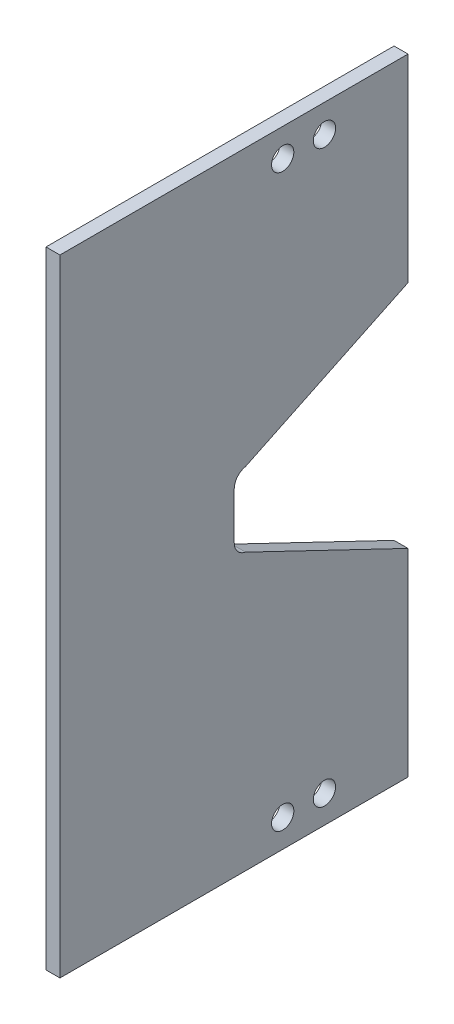
SolidWorks part; units mm, degrees
material "ABS"
ref_plane "前视基准面" through (0, 0, 0) normal (0, 0, 1) x (1, 0, 0)
ref_plane "上视基准面" through (0, 0, 0) normal (0, 1, 0) x (1, 0, 0)
ref_plane "右视基准面" through (0, 0, 0) normal (1, 0, 0) x (0, 0, -1)
ref_plane "基准面4" through (-0.7938, 0, 0) normal (-1, 0, 0) x (0, -1, 0)
sketch "草图1" plane through (-0.7938, 0, 0) normal (-1, 0, 0) x (0, -1, 0)
  line L1 (38.795, 5) -> (12.795, 5)
  line L2 (10.795, 3) -> (10.795, -13)
  line L5 (10.795, 3) -> (55.77, 3) construction
  line L6 (55.77, 3) -> (55.77, -5.0783) construction
  line L7 (55.77, 3) -> (55.77, 5) construction
  line L13 (38.795, 5) -> (72.745, 5)
  line L15 (100.745, 3) -> (100.745, -13)
  line L18 (72.745, 5) -> (98.745, 5)
  line L19 (55.77, 5) -> (55.77, -5.0783) construction
  line L20 (55.77, -5.0783) -> (55.77, -0.0391) construction
  line L21 (55.77, -0.0391) -> (65.77, -0.0391) construction
  line L22 (72.112, -14.1547) -> (62.1308, -0.0391) construction
  line L31 (13.295, -15) -> (13.295, -10) construction
  line L32 (13.295, 0) -> (13.295, -15) construction
  line L33 (18.295, 0) -> (18.295, -15) construction
  line L34 (18.295, -15) -> (18.295, -10) construction
  line L35 (93.245, 0) -> (93.245, -15) construction
  line L36 (93.245, -15) -> (93.245, -10) construction
  line L37 (93.245, -10) -> (98.245, -10) construction
  line L38 (55.77, -0.0391) -> (50.77, -0.0391)
  line L39 (55.77, -0.0391) -> (60.77, -0.0391)
  line L40 (12.795, -15) -> (47.795, -15)
  line L41 (98.745, -15) -> (63.745, -15)
  line L42 (50.77, -0.0391) -> (47.795, -15)
  line L43 (60.77, -0.0391) -> (63.745, -15)
  arc A2 (12.795, 5) -> (10.795, 3) centre (12.795, 3) ccw
  arc A3 (10.795, -13) -> (12.795, -15) centre (12.795, -13) ccw
  arc A12 (98.745, 5) -> (100.745, 3) centre (98.745, 3) cw
  arc A13 (100.745, -13) -> (98.745, -15) centre (98.745, -13) cw
extrude "凸台-拉伸1" add sketch "草图1" against normal blind 2
fillet "圆角1" radius 2 1 edges at (0.2063, -47.795, -15)
fillet "圆角2" radius 2 1 edges at (0.2062, -50.77, -0.0391)
fillet "圆角3" radius 2 1 edges at (0.2062, -60.77, -0.0391)
fillet "圆角4" radius 2 1 edges at (0.2063, -63.745, -15)
sketch "草图2" plane through (1.2062, 0, 0) normal (1, 0, 0) x (0, 0, -1)
  line L0 (-5, -55.77) -> (-15, -55.77) construction
  line L2 (-5, -98.745) -> (-5, -12.795) construction
  line L3 (-15, -55.77) -> (-15, -100.745) construction
  line L4 (-15, -100.745) -> (-3, -100.745) construction
  line L5 (-3, -100.745) -> (-3, -10.795) construction
  line L6 (-3, -10.795) -> (-15, -10.795) construction
  line L7 (-15, -10.795) -> (-15, -55.77) construction
  line L8 (-15, -10.795) -> (-3, -10.795)
  line L9 (-3, -10.795) -> (-3, -100.745)
  line L10 (-3, -100.745) -> (-15, -100.745)
  line L11 (-15, -100.745) -> (-15, -10.795)
  line L12 (15, -29.4743) -> (25, -29.4743) construction
  line L13 (15, -12.795) -> (15, -46.1535) construction
  line L14 (25, -29.4743) -> (25, -82.0657) construction
  line L15 (25, -82.0657) -> (15, -82.0657) construction
  line L16 (15, -65.3865) -> (15, -98.745) construction
  line L17 (15, -82.0657) -> (15, -100.745) construction
  line L18 (25, -82.0657) -> (25, -100.745) construction
  line L19 (25, -100.745) -> (13, -100.745) construction
  line L20 (13, -100.745) -> (-3, -100.745) construction
  line L21 (13, -100.745) -> (13, -10.795) construction
  line L22 (13, -10.795) -> (25, -10.795) construction
  line L23 (25, -10.795) -> (25, -29.4743) construction
  line L24 (1.6491, -50.4499) -> (13.3901, -48.1151) construction
  line L25 (13.3901, -48.1151) -> (25, -45.8065) construction
  line L26 (1.6491, -61.0901) -> (13.3901, -63.4249) construction
  line L27 (13.3901, -63.4249) -> (25, -65.7335) construction
  line L28 (13.3901, -48.1151) -> (25, -45.8065)
  line L29 (25, -45.8065) -> (25, -10.795)
  line L30 (25, -10.795) -> (13, -10.795)
  line L31 (13, -10.795) -> (13.3901, -48.1151)
  line L32 (13.3901, -63.4249) -> (25, -65.7335)
  line L33 (25, -65.7335) -> (25, -100.745)
  line L34 (25, -100.745) -> (13, -100.745)
  line L35 (13, -100.745) -> (13.3901, -63.4249)
  arc A0 (13, -100.745) -> (15, -98.745) centre (13, -98.745) ccw construction
extrude "凸台-拉伸2" add sketch "草图2" against normal blind 2
sketch "草图5" plane through (1.2062, 0, 0) normal (1, 0, 0) x (0, 0, -1)
  line L0 (25, -45.8065) -> (25, -10.795) construction
  line L1 (25, -10.795) -> (25, -28.3007) construction
  line L2 (25, -28.3007) -> (25, -45.8065) construction
  line L3 (25, -45.8065) -> (25, -37.0536) construction
  line L4 (25, -37.0536) -> (25, -41.43) construction
  line L5 (25, -41.43) -> (1.6491, -50.4499) construction
  line L7 (1.6491, -50.4499) -> (25, -45.8065)
  line L9 (0.0391, -55.77) -> (-15, -55.77) construction
  line L10 (0.0391, -52.4115) -> (0.0391, -59.1285) construction
  line L11 (-15, -10.795) -> (-15, -100.745) construction
  line L15 (25, -41.43) -> (25, -37.0536) construction
  line L16 (25, -37.0536) -> (25, -39.2418) construction
  line L17 (25, -39.2418) -> (1.6491, -50.4499) construction
  line L18 (1.6491, -50.4499) -> (25, -39.2418)
  line L19 (25, -39.2418) -> (25, -45.8065)
  line L20 (1.6491, -61.0901) -> (25, -72.2982)
  line L21 (1.6491, -61.0901) -> (25, -65.7335)
  line L22 (25, -72.2982) -> (25, -65.7335)
extrude "切除-拉伸1" cut sketch "草图5" against normal blind 10
sketch "草图6" plane through (1.2062, 0, 0) normal (1, 0, 0) x (0, 0, -1)
  line L0 (-15, -10.795) -> (10, -10.795) construction
  line L2 (-15, -10.795) -> (25, -10.795) construction
  line L3 (10, -10.795) -> (10, -14.795) construction
  line L4 (10, -14.795) -> (13, -14.795) construction
  line L5 (-15, -55.77) -> (0.0391, -55.77) construction
  line L6 (-15, -10.795) -> (-15, -100.745) construction
  line L7 (0.0391, -52.4115) -> (0.0391, -59.1285) construction
  circle A0 centre (13, -14.795) radius 1.6
  circle A1 centre (7, -14.795) radius 1.6
  circle A2 centre (13, -96.745) radius 1.6
  circle A3 centre (7, -96.745) radius 1.6
extrude "切除-拉伸2" cut sketch "草图6" against normal blind 10
sketch "草图7" plane through (-0.7938, 0, 0) normal (-1, 0, 0) x (0, 0, 1)
  line L0 (15, -10.795) -> (25, -10.795) construction
  line L1 (15, -100.745) -> (25, -100.745) construction
  line L2 (25, -100.745) -> (25, -10.795) construction
  line L3 (15, -10.795) -> (25, -10.795)
  line L4 (25, -10.795) -> (25, -100.745)
  line L5 (25, -100.745) -> (15, -100.745)
  line L6 (15, -100.745) -> (15, -10.795)
extrude "凸台-拉伸3" add sketch "草图7" against normal blind 2
